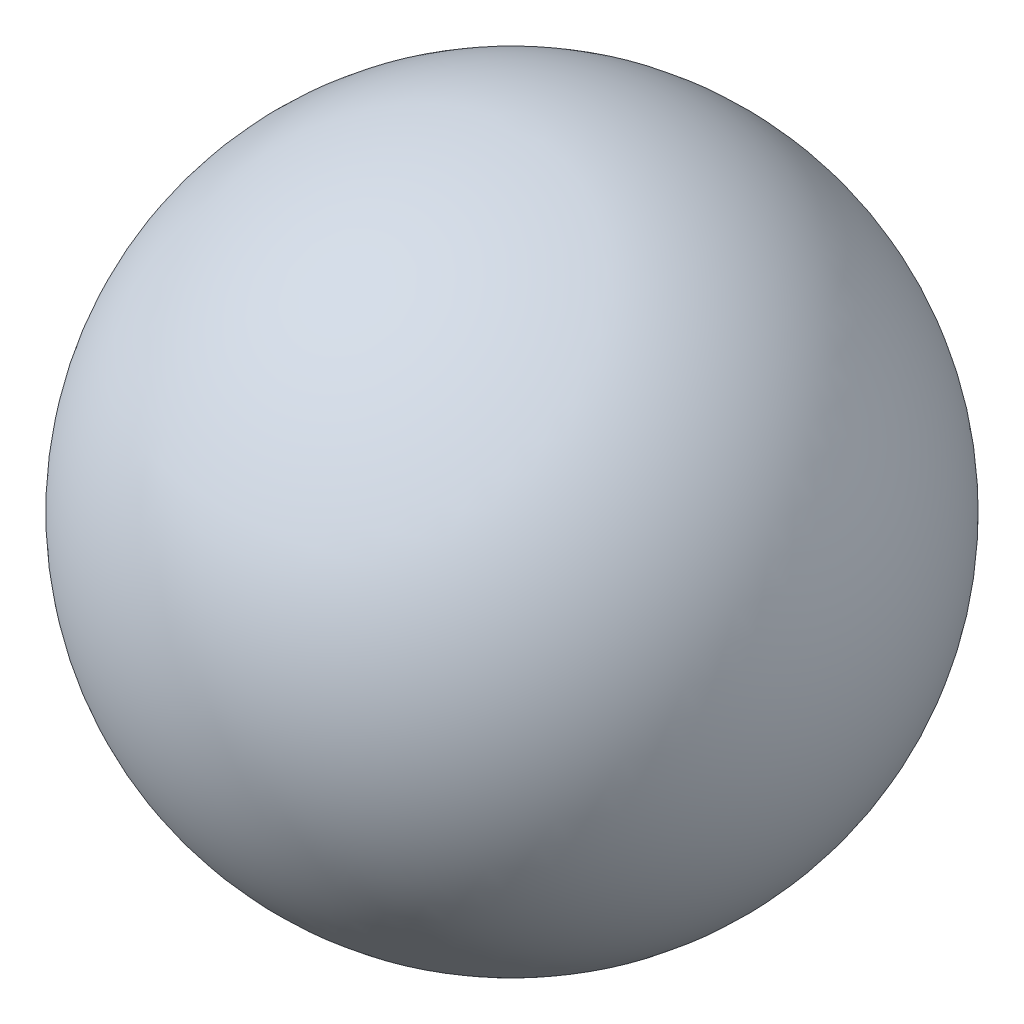
SolidWorks part; units mm, degrees
ref_plane "Front Plane" through (0, 0, 0) normal (0, 0, 1) x (1, 0, 0)
ref_plane "Top Plane" through (0, 0, 0) normal (0, 1, 0) x (1, 0, 0)
ref_plane "Right Plane" through (0, 0, 0) normal (1, 0, 0) x (0, 0, -1)
sketch "Sketch1" plane through (0, 0, 0) normal (0, 0, 1) x (1, 0, 0)
  line L0 (0, -20) -> (0, 20) construction
  circle A0 centre (0, 0) radius 20
  dimension "D1" = 40
revolve "Revolve1" add sketch "Sketch1" angle 360 about L0
